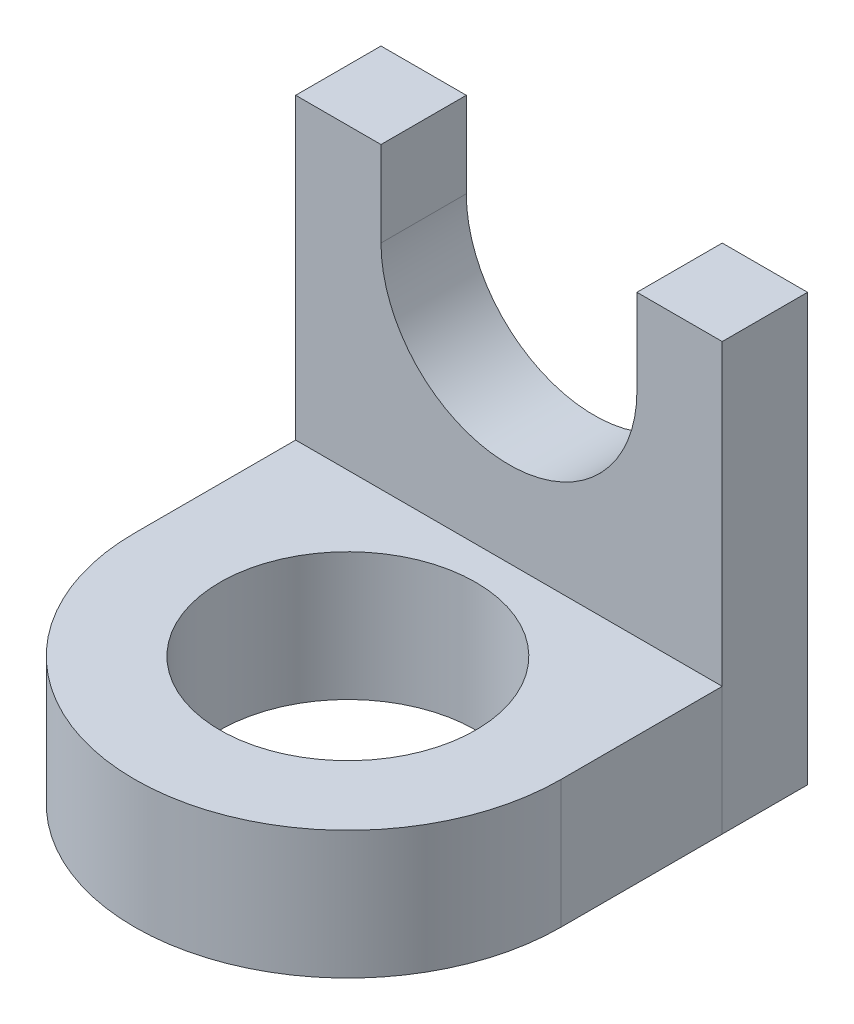
SolidWorks part; units mm, degrees
ref_plane "Front" through (0, 0, 0) normal (0, 0, 1) x (1, 0, 0)
ref_plane "Top" through (0, 0, 0) normal (0, 1, 0) x (1, 0, 0)
ref_plane "Right" through (0, 0, 0) normal (1, 0, 0) x (0, 0, -1)
sketch "Sketch1" plane through (0, 0, 0) normal (0, 0, 1) x (1, 0, 0)
  line L1 (-5, -5) -> (5, -5)
  line L2 (-5, -5) -> (-5, 5)
  line L3 (-5, 5) -> (-3, 5)
  line L4 (5, -5) -> (5, 5)
  line L5 (-5, -5) -> (5, 5) construction
  line L6 (-5, 5) -> (5, -5) construction
  line L7 (3, 5) -> (3, 3)
  line L8 (-3, 5) -> (-3, 3)
  line L9 (3, 5) -> (5, 5)
  arc A1 (-3, 3) -> (3, 3) centre (0, 3) ccw
  point P0 (0, 0)
  point P8 (0, 4)
  dimension "D4" = 3
  dimension "D1" = 10
  dimension "D2" = 10
  dimension "D3" = 2
extrude "Boss-Extrude1" add sketch "Sketch1" along normal blind 2
sketch "Sketch2" plane through (0, -5, 0) normal (0, -1, 0) x (1, 0, 0)
  line L1 (-5, 2) -> (5, 2)
  line L2 (-5, 2) -> (-5, 5.7765)
  line L4 (5, 2) -> (5, 5.7765)
  arc A0 (-5, 5.7765) -> (5, 5.7765) centre (0, 5.7765) cw
  circle A1 centre (0, 5.7765) radius 3
  dimension "D1" = 5
  dimension "D3" = 6
  dimension "D2" = 10
extrude "Boss-Extrude2" add sketch "Sketch2" against normal blind 3 separate body
